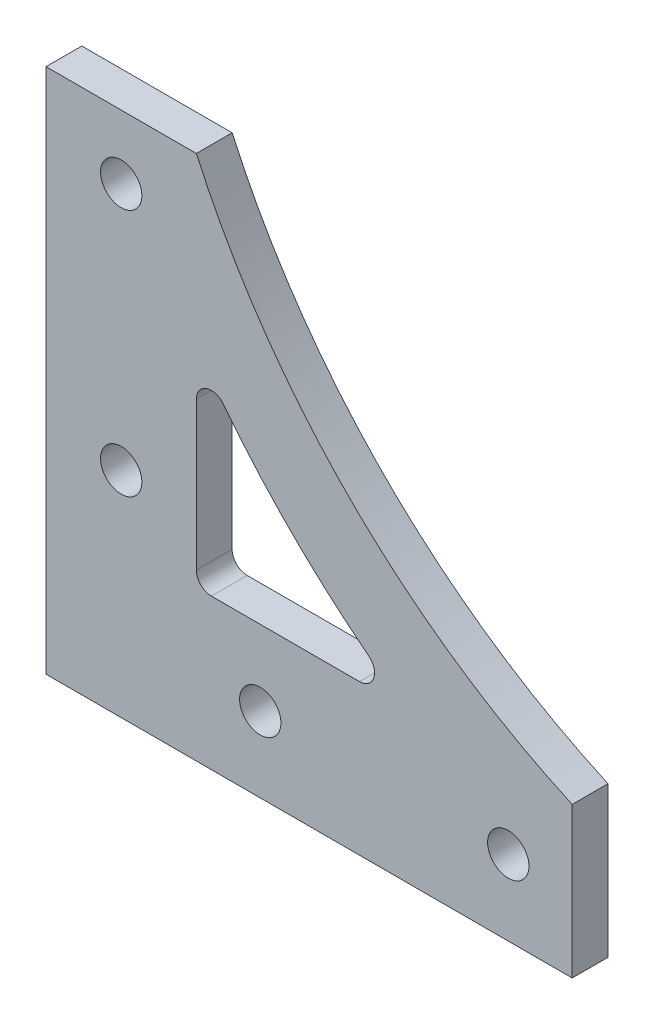
SolidWorks part; units mm, degrees
ref_plane "Front Plane" through (0, 0, 0) normal (0, 0, 1) x (1, 0, 0)
ref_plane "Top Plane" through (0, 0, 0) normal (0, 1, 0) x (1, 0, 0)
ref_plane "Right Plane" through (0, 0, 0) normal (1, 0, 0) x (0, 0, -1)
sketch "Sketch1" plane through (0, 0, 0) normal (0, 0, 1) x (1, 0, 0)
  line L0 (0, 0) -> (70, 0)
  line L1 (70, 0) -> (70, 20)
  line L2 (0, 0) -> (0, 70)
  line L3 (0, 70) -> (20, 70)
  line L4 (20, 41.7004) -> (20, 22)
  line L5 (22, 20) -> (41.7004, 20)
  line L6 (70, 10) -> (10, 10) construction
  line L7 (10, 10) -> (10, 70) construction
  arc A0 (20, 70) -> (70, 20) centre (111.1438, 111.1438) ccw
  arc A1 (23.5778, 42.9295) -> (42.9295, 23.5778) centre (111.1438, 111.1438) ccw
  circle A2 centre (10, 61.5) radius 2.75
  circle A3 centre (10, 28.5) radius 2.75
  circle A4 centre (28.5, 10) radius 2.75
  circle A5 centre (61.5, 10) radius 2.75
  arc A6 (41.7004, 20) -> (42.9295, 23.5778) centre (41.7004, 22) ccw
  arc A7 (20, 22) -> (22, 20) centre (22, 22) ccw
  arc A8 (20, 41.7004) -> (23.5778, 42.9295) centre (22, 41.7004) cw
  dimension "D6" = 100
  dimension "D7" = 11
  dimension "D10" = 5.5
  dimension "D13" = 2
  dimension "D1" = 20
  dimension "D2" = 70
  dimension "D3" = 70
  dimension "D4" = 20
  dimension "D5" = 20
  dimension "D8" = 8.5
  dimension "D9" = 33
  dimension "D11" = 33
  dimension "D12" = 8.5
extrude "Boss-Extrude1" add sketch "Sketch1" along normal blind 4.7625
